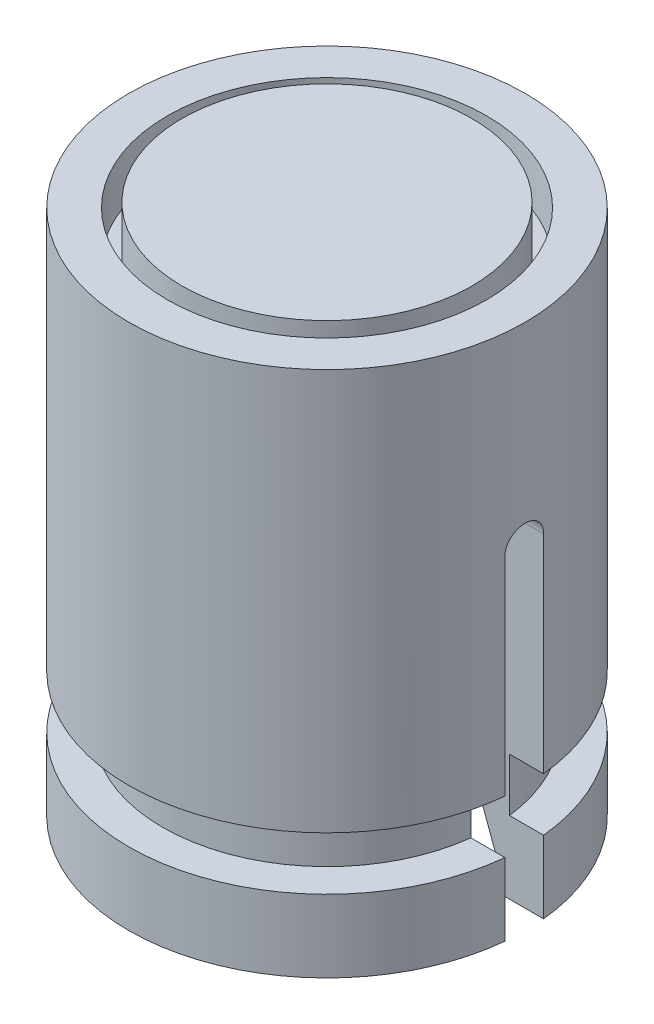
SolidWorks part; units mm, degrees
ref_plane "Płaszczyzna przednia" through (0, 0, 0) normal (0, 0, 1) x (1, 0, 0)
ref_plane "Płaszczyzna górna" through (0, 0, 0) normal (0, 1, 0) x (1, 0, 0)
ref_plane "Płaszczyzna prawa" through (0, 0, 0) normal (1, 0, 0) x (0, 0, -1)
sketch "Szkic2" plane through (0, 0, 0) normal (1, 0, 0) x (0, 0, -1)
  line L0 (-3.3, 10.9) -> (-3.3, 9.9)
  line L1 (-3.1428, 0) -> (-4.1, 0)
  line L3 (0, 11) -> (-3, 11)
  line L4 (-4.1, 0) -> (-4.1, 1.5)
  line L5 (-3.3, 9.9) -> (-3, 9.9)
  line L6 (-3, 9.9) -> (-3, 11)
  line L8 (-4.1, 2.6) -> (-3.4, 2.6)
  line L9 (-3.4, 2.6) -> (-3.4, 1.5)
  line L10 (-3.4, 1.5) -> (-4.1, 1.5)
  line L12 (-3.1428, 0) -> (-3.1428, 0.6)
  line L13 (-3.3, 10.9) -> (-4.1, 10.9)
  line L14 (-4.1, 2.6) -> (-4.1, 10.9)
  line L15 (-2.85, 1.4046) -> (-2.85, 7.4)
  line L16 (-2.85, 7.4) -> (-1.35, 7.4)
  line L19 (-1.35, 7.4) -> (-1.35, 8.6)
  line L20 (-1.35, 8.6) -> (0, 8.6)
  line L23 (-3.1428, 0.6) -> (-2.85, 1.4046)
  line L24 (0, 8.6) -> (0, 11)
  line L25 (0, 0) -> (0, -1004.0986) construction
  line L26 (-7.0309, 0) -> (7.2241, 0) construction
  dimension "D1" = 11
  dimension "D2" = 4.1
  dimension "D3" = 0.8
  dimension "D4" = 0.3
  dimension "D5" = 1
  dimension "D6" = 0.1
  dimension "D7" = 2.85
  dimension "D8" = 1.5
  dimension "D9" = 8.3
  dimension "D10" = 0.7
  dimension "D11" = 7.4
  dimension "D12" = 8.6
  dimension "D13" = 1.5
  dimension "D14" = 0.9572
  dimension "D15" = 160
  dimension "D16" = 0.6
revolve "Obrót1" add sketch "Szkic2" angle 360 about L25
sketch "Szkic3" plane through (0, 0, 0) normal (1, 0, 0) x (0, 0, -1)
  line L0 (0, 0) -> (0, 6.9) construction
  line L1 (-0.4, 0) -> (-0.4, 6.9)
  line L2 (0.4, 0) -> (0.4, 6.9)
  line L3 (-0.4, 0) -> (0.4, 0)
  line L4 (-4.1, 0) -> (4.1, 0) construction
  arc A1 (0.4, 6.9) -> (-0.4, 6.9) centre (0, 6.9) ccw
  point P3 (0, 3.0998)
  dimension "D1" = 0.8
  dimension "D2" = 6.9
extrude "Wytnij-wyciągnięcie1" cut sketch "Szkic3" against normal through all and the other way through all
